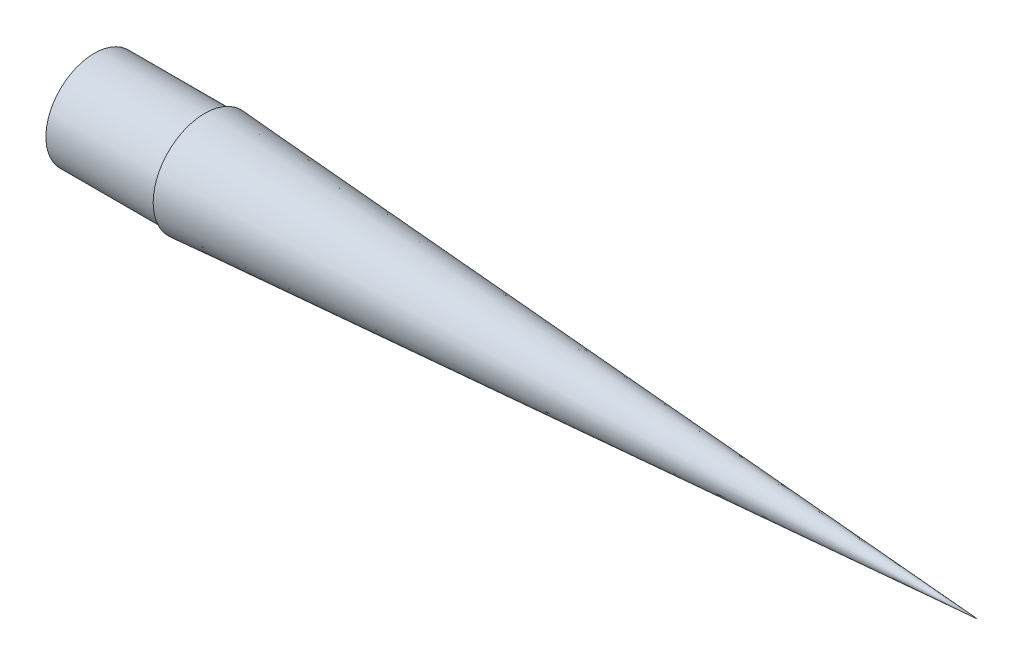
SolidWorks part; units mm, degrees
ref_plane "Front Plane" through (0, 0, 0) normal (0, 0, 1) x (1, 0, 0)
ref_plane "Top Plane" through (0, 0, 0) normal (0, 1, 0) x (1, 0, 0)
ref_plane "Right Plane" through (0, 0, 0) normal (1, 0, 0) x (0, 0, -1)
sketch "Sketch1" plane through (0, 0, 0) normal (0, 1, 0) x (1, 0, 0)
  line L1 (0, 22.225) -> (50.8, 22.225)
  line L2 (50.8, 22.225) -> (50.8, 23.6982)
  line L3 (50.8, 23.6982) -> (406.4, 0)
  line L4 (406.4, 0) -> (387.3009, 0)
  line L9 (52.07, 20.955) -> (52.07, 22.3407)
  line L10 (1.27, 1.27) -> (1.27, 20.955) construction
  line L11 (0, 0) -> (0, 22.225) construction
  line L12 (1.27, 20.955) -> (52.07, 20.955) construction
  line L13 (368.2441, 1.27) -> (1.27, 1.27) construction
  line L14 (52.07, 22.3407) -> (387.3009, 0)
  line L15 (52.07, 20.955) -> (0, 20.955)
  line L16 (0, 20.955) -> (0, 22.225)
  line L19 (52.07, 22.3407) -> (368.2441, 1.27) construction
  line L20 (406.4, 0) -> (0, 0) construction
  dimension "D2" = 50.8
  dimension "D4" = 23.6982
  dimension "D5" = 1.27
revolve "Revolve3" add sketch "Sketch1" angle 360 about L4
